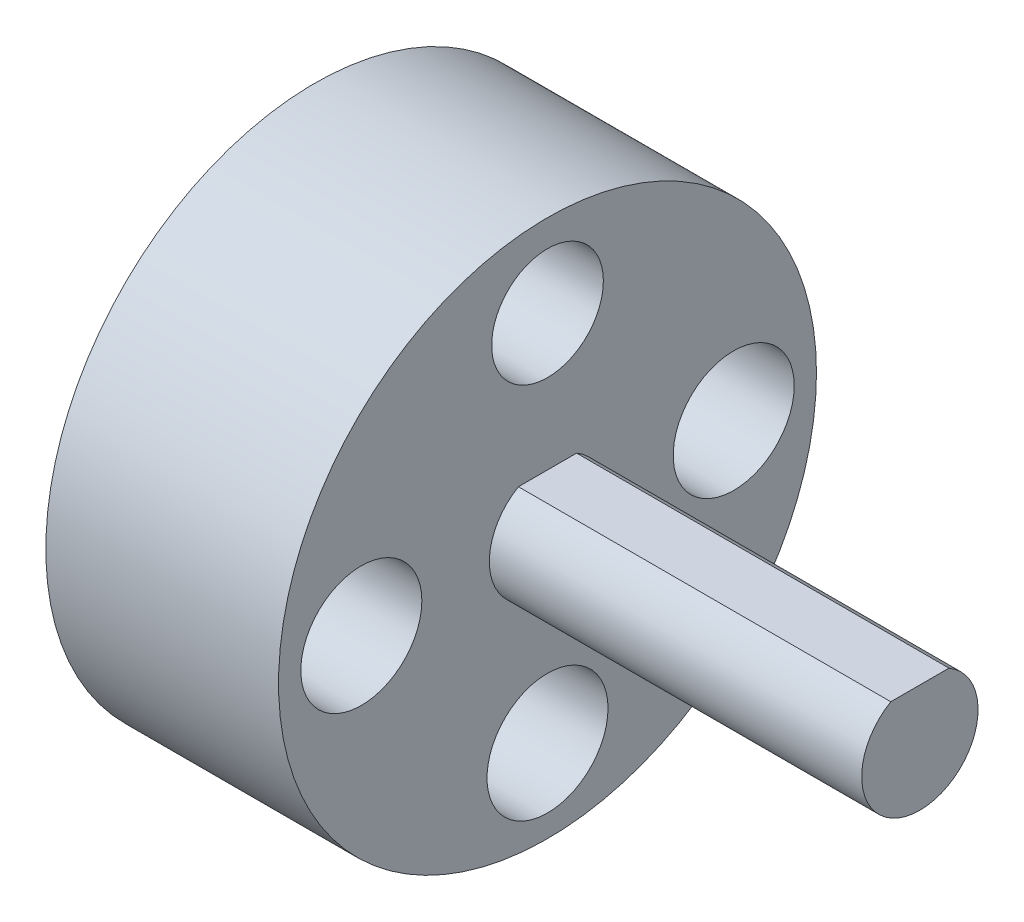
SolidWorks part; units mm, degrees
ref_plane "Front Plane" through (0, 0, 0) normal (0, 0, 1) x (1, 0, 0)
ref_plane "Top Plane" through (0, 0, 0) normal (0, 1, 0) x (1, 0, 0)
ref_plane "Right Plane" through (0, 0, 0) normal (1, 0, 0) x (0, 0, -1)
sketch "Sketch1" plane through (0, 0, 0) normal (1, 0, 0) x (0, 0, -1)
  circle A0 centre (0, 0) radius 11.557
  circle A1 centre (0, 0) radius 2.5 construction
  circle A2 centre (0, 8) radius 2.6
  circle A3 centre (8, 0) radius 2.6
  circle A4 centre (0, -8) radius 2.6
  circle A5 centre (-8, 0) radius 2.6
  circle B0 centre (0, -8) radius 2.4
  circle B1 centre (8, 0) radius 2.4
  circle B2 centre (-8, 0) radius 2.4
  circle B3 centre (0, 8) radius 2.4
  dimension "D1" = 23.114
  dimension "D2" = 5
  dimension "D3" = 0.2
sketch_block_instance "Block-LARGEMOTORTURN-1"
sketch_block "Block-LARGEMOTORTURN"
extrude "Boss-Extrude1" add sketch "Sketch1" along normal blind 10 contours A0 B3 B2 B1 B0 A1 | A1
sketch "Sketch2" plane through (10, 0, 0) normal (1, 0, 0) x (0, 0, -1)
  line L0 (-1.25, 2.1651) -> (1.25, 2.1651)
  circle A0 centre (0, 0) radius 2.5 construction
  circle A1 centre (0, 0) radius 2.5
  dimension "D1" = 2.5
extrude "Boss-Extrude2" add sketch "Sketch2" along normal blind 16 contours L0 A1
